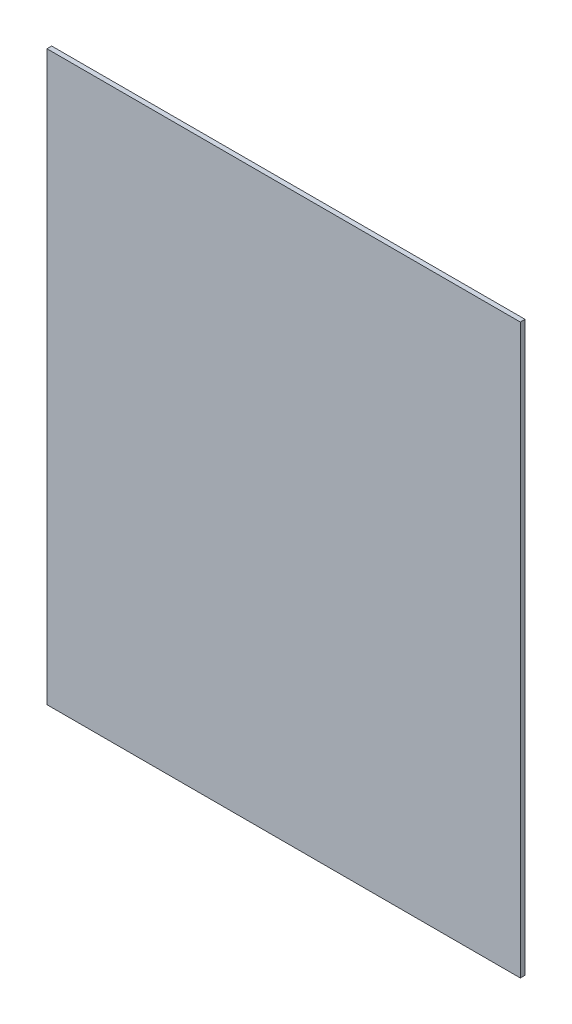
SolidWorks part; units mm, degrees
ref_plane "Front Plane" through (0, 0, 0) normal (0, 0, 1) x (1, 0, 0)
ref_plane "Top Plane" through (0, 0, 0) normal (0, 1, 0) x (1, 0, 0)
ref_plane "Right Plane" through (0, 0, 0) normal (1, 0, 0) x (0, 0, -1)
sketch "Croquis1" plane through (0, 0, 0) normal (0, 0, 1) x (1, 0, 0)
  line L0 (-250, -300) -> (-250, 300)
  line L1 (-250, -300) -> (250, -300)
  line L2 (-250, 300) -> (250, 300)
  line L3 (250, -300) -> (250, 300)
  line L4 (-250, -300) -> (250, 300) construction
  line L5 (-250, 300) -> (250, -300) construction
  point P1 (0, 0)
  dimension "D1" = 600
  dimension "D2" = 500
extrude "Saliente-Extruir1" add sketch "Croquis1" along normal blind 5
